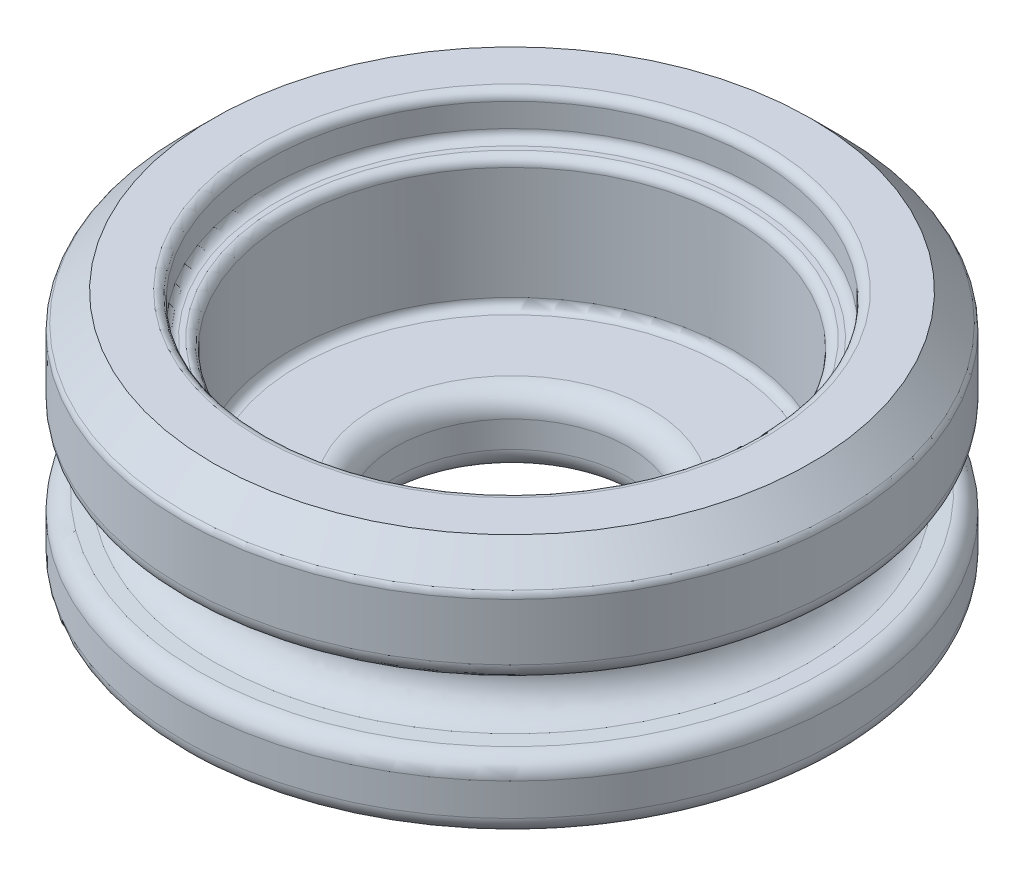
SolidWorks part; units mm, degrees
ref_plane "Front Plane" through (0, 0, 0) normal (0, 0, 1) x (1, 0, 0)
ref_plane "Top Plane" through (0, 0, 0) normal (0, 1, 0) x (1, 0, 0)
ref_plane "Right Plane" through (0, 0, 0) normal (1, 0, 0) x (0, 0, -1)
sketch "Sketch2" plane through (0, 0, 0) normal (0, 1, 0) x (1, 0, 0)
  circle A0 centre (0, 0) radius 6.477 construction
  circle A1 centre (0, 0) radius 9.525
  dimension "D1" = 12.954
  dimension "D2" = 19.05
extrude "Boss-Extrude1" add sketch "Sketch2" along normal blind 6.985
sketch "Sketch3" plane through (0, 6.985, 0) normal (0, 1, 0) x (1, 0, 0)
  circle A0 centre (0, 0) radius 6.4135
  dimension "D1" = 12.827
extrude "Cut-Extrude1" cut sketch "Sketch3" against normal up to surface (6.985 mm away) up to face at (0, 0, 9.525)
sketch "Sketch4" plane through (0, 6.985, 0) normal (0, 1, 0) x (1, 0, 0)
  circle A0 centre (0, 0) radius 7.0723
  dimension "D1" = 14.1446
extrude "Cut-Extrude2" cut sketch "Sketch4" against normal blind 1.1906
ref_plane "Plane1" through (0, 2.8972, 0) normal (0, 1, 0) x (1, 0, 0)
sketch "Sketch5" plane through (0, 2.8972, 0) normal (0, 1, 0) x (1, 0, 0)
  circle A0 centre (0, 0) radius 9.525
  circle A1 centre (0, 0) radius 9.525 construction
sketch3d "3DSketch1"
  line L0 (0.7605, 2.8972, 9.4946) -> (0.7605, 3.8497, 9.4946) construction
  line L1 (0.7605, 2.8972, 9.4946) -> (0.7605, 1.9447, 9.4946) construction
  line L2 (0.7605, 2.8972, 9.4946) -> (0.7605, 2.9021, 8.5421) construction
  line L3 (0.7605, 2.9021, 8.5421) -> (0.7605, 3.8416, 8.5421) construction
  line L4 (0.7605, 2.9021, 8.5421) -> (0.7605, 1.961, 8.5421) construction
  line L5 (0.7605, 3.8416, 8.5421) -> (0.7605, 3.8497, 9.4946) construction
  line L6 (0.7605, 1.961, 8.5421) -> (0.7605, 1.9447, 9.4946) construction
  line L7 (0.7605, 3.8416, 8.5421) -> (0.7605, 3.8497, 9.4946)
  line L8 (0.7605, 3.8497, 9.4946) -> (0.7605, 1.9447, 9.4946)
  line L9 (0.7605, 1.9447, 9.4946) -> (0.7605, 1.961, 8.5421)
  circle A0 centre (0.7605, 2.8972, 9.4946) radius 0.9525 construction
  circle A1 centre (0, 2.8972, 0) radius 9.525 construction
  circle A2 centre (0.7605, 2.9013, 8.6942) radius 0.9525 construction
  arc A3 (0.7605, 1.961, 8.5421) -> (0.7605, 3.8416, 8.5421) centre (0.7605, 2.9013, 8.6942) cw
  point P2 (1.713, 2.8972, 9.4946)
  point P5 (0, 12.4222, 0)
  point P11 (1.713, 2.9013, 8.6942)
  point P15 (1.713, 2.9013, 8.6942)
  dimension "D1" = 1.905
sweep "Cut-Sweep1" cut profiles "3DSketch1" path "Sketch5"
sketch "Sketch6" plane through (0, 0, 0) normal (0, -1, 0) x (1, 0, 0)
  circle A0 centre (0, 0) radius 6.4135
  circle A1 centre (0, 0) radius 3.3655
  circle A2 centre (0, 0) radius 6.4135 construction
  dimension "D1" = 6.731
extrude "Boss-Extrude2" add sketch "Sketch6" against normal blind 2.032
fillet "Fillet1" radius 0.254 3 edges at (0, 6.985, 7.0723) (0, 5.7944, 7.0723) (0, 5.7944, 6.4135)
fillet "Fillet2" radius 0.508 3 edges at (0, 0, 9.525) (0.7605, 3.8497, 9.4946) (0.7605, 1.9447, 9.4946)
chamfer "Chamfer1" distance 0.889 angle 45 1 edges at (0, 6.985, 9.525)
fillet "Fillet3" radius 0.254 1 edges at (0, 6.096, 9.525)
fillet "Fillet4" radius 0.635 2 edges at (0, 2.032, -3.3655) (0, 0, -3.3655)
fillet "Fillet5" radius 0.254 1 edges at (0, 2.032, -6.4135)
